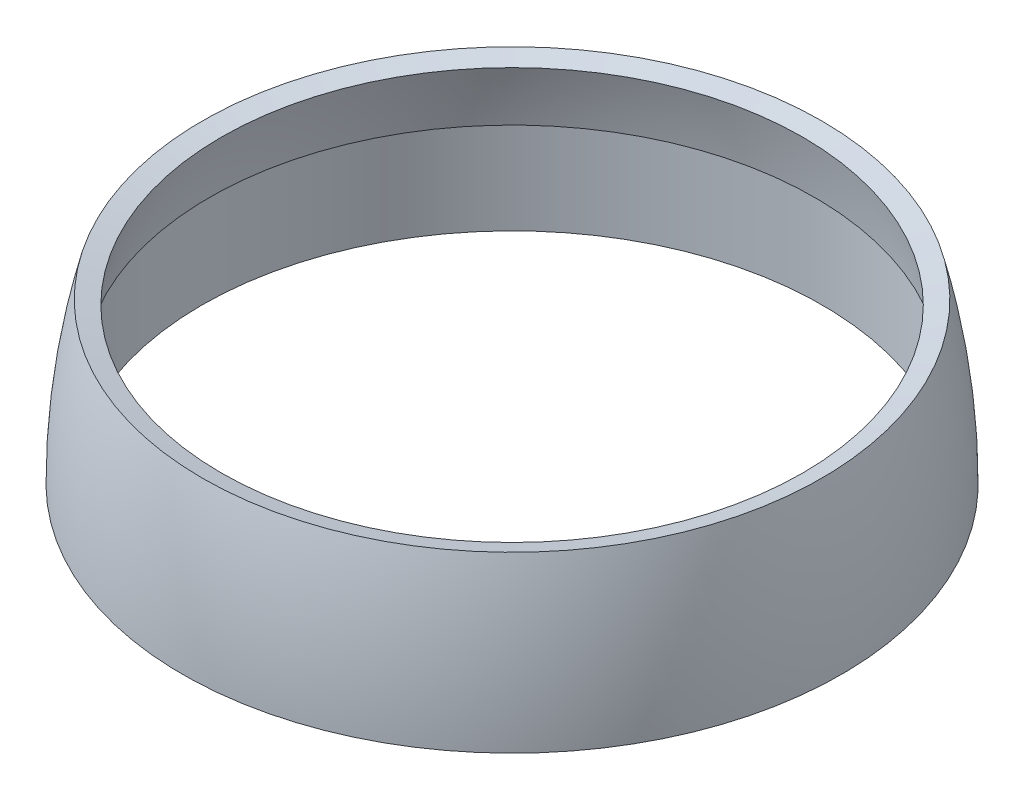
SolidWorks part; units mm, degrees
material "Plain Carbon Steel"
ref_plane "Front Plane" through (0, 0, 0) normal (0, 0, 1) x (1, 0, 0)
ref_plane "Top Plane" through (0, 0, 0) normal (0, 1, 0) x (1, 0, 0)
ref_plane "Right Plane" through (0, 0, 0) normal (1, 0, 0) x (0, 0, -1)
sketch "Sketch1" plane through (0, 0, 0) normal (0, 1, 0) x (1, 0, 0)
  circle A0 centre (0, 0) radius 16
  dimension "D1" = 32
sketch "Sketch2" plane through (0, 0, 0) normal (0, 0, 1) x (1, 0, 0)
  line L0 (15, 8) -> (-8.4558, 8) construction
  line L8 (0, 0) -> (0, 23.5897) construction
  line L13 (0, 0) -> (16, 0) construction
  line L14 (16, 0) -> (16, -6.6635) construction
  arc A0 (15, 8) -> (16, 0) centre (-16.5, 0) cw
  dimension "D1" = 8
  dimension "D2" = 1
revolve "Revolve-Thin1" add sketch "Sketch2" angle 360 about L8 wall 1
sketch "Sketch3" plane through (0, 0, 0) normal (0, 0, 1) x (1, 0, 0)
  line L0 (16, 0) -> (16, 5)
  line L1 (-17, 0) -> (17, 0) construction
  line L2 (16, 5) -> (0, 5)
  line L3 (0, 5) -> (0, 0) construction
  line L4 (0, 0) -> (16, 0)
  line L5 (-16, 0) -> (16, 0) construction
  line L6 (0, 5) -> (0, 0)
  arc A0 (16, 0) -> (15, 8) centre (-16.5, 0) ccw construction
  dimension "D1" = 5
revolve "Cut-Revolve1" cut sketch "Sketch3" angle 360 about L3
